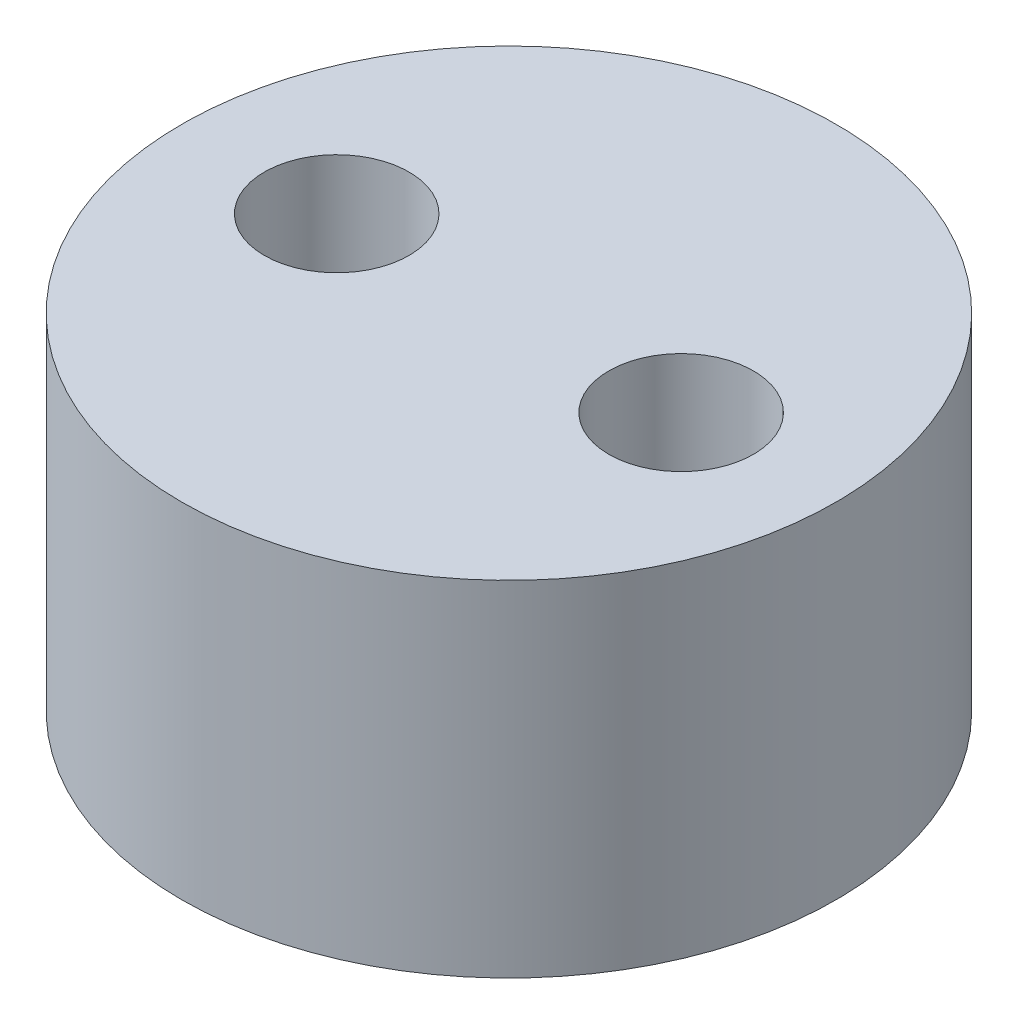
SolidWorks part; units mm, degrees
ref_plane "Front Plane" through (0, 0, 0) normal (0, 0, 1) x (1, 0, 0)
ref_plane "Top Plane" through (0, 0, 0) normal (0, 1, 0) x (1, 0, 0)
ref_plane "Right Plane" through (0, 0, 0) normal (1, 0, 0) x (0, 0, -1)
sketch "Sketch1" plane through (0, 0, 0) normal (0, 1, 0) x (1, 0, 0)
  circle A0 centre (0, 0) radius 9.5
  dimension "D1" = 19
extrude "Boss-Extrude1" add sketch "Sketch1" along normal blind 10
sketch "Sketch2" plane through (0, 10, 0) normal (0, 1, 0) x (1, 0, 0)
  line L0 (0, 0) -> (5, 0) construction
  circle A0 centre (5, 0) radius 2.1
  dimension "D1" = 4.2
  dimension "D2" = 5
extrude "Cut-Extrude1" cut sketch "Sketch2" against normal through all and the other way through all
mirror "Mirror1" about plane through (0, 0, 0) normal (1, 0, 0) of "Cut-Extrude1"
